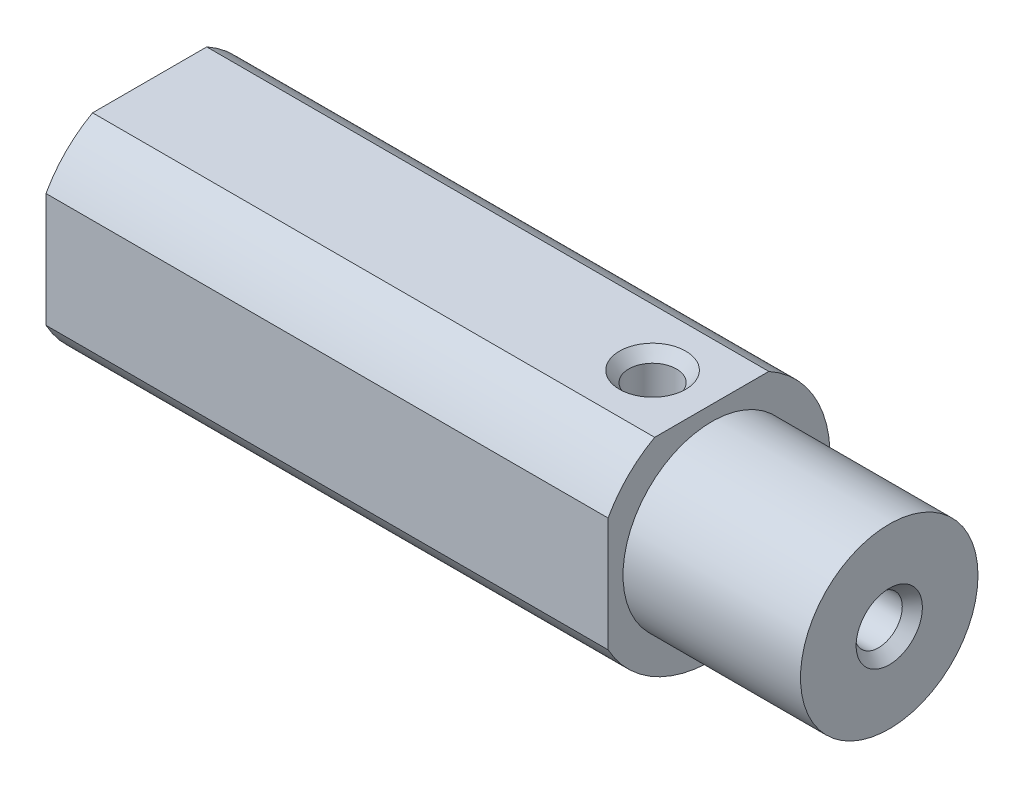
SolidWorks part; units mm, degrees
ref_plane "Front Plane" through (0, 0, 0) normal (0, 0, 1) x (1, 0, 0)
ref_plane "Top Plane" through (0, 0, 0) normal (0, 1, 0) x (1, 0, 0)
ref_plane "Right Plane" through (0, 0, 0) normal (1, 0, 0) x (0, 0, -1)
sketch "Sketch1" plane through (0, 0, 0) normal (1, 0, 0) x (0, 0, -1)
  circle A0 centre (0, 0) radius 12.7
extrude "Boss-Extrude1" add sketch "Sketch1" against normal blind 79.375
sketch "Sketch2" plane through (0, 0, 0) normal (1, 0, 0) x (0, 0, -1)
  circle A0 centre (0, 0) radius 9.525
  circle A1 centre (0, 0) radius 21.2934
extrude "Cut-Extrude1" cut sketch "Sketch2" against normal blind 19.05
ref_plane "Plane1" through (0, 0, 11.1252) normal (0, 0, 1) x (1, 0, 0)
sketch "Sketch3" plane through (0, 12.4012, 11.1252) normal (0, 0, 1) x (1, 0, 0)
  line L1 (-91.2436, 24.1614) -> (-2.896, 24.1614)
  line L2 (-91.2436, 24.1614) -> (-91.2436, -37.9233)
  line L3 (-91.2436, -37.9233) -> (-2.896, -37.9233)
  line L4 (-2.896, 24.1614) -> (-2.896, -37.9233)
extrude "Cut-Extrude2" cut sketch "Sketch3" along normal blind 7.62
ref_plane "Plane3" through (0, 11.1252, 0) normal (0, 1, 0) x (-1, 0, 0)
sketch "Sketch7" plane through (0, 11.1252, 0) normal (0, 1, 0) x (-1, 0, 0)
  line L1 (96.4133, -27.0383) -> (-22.4115, -27.0383)
  line L2 (96.4133, -27.0383) -> (96.4133, 24.8097)
  line L3 (96.4133, 24.8097) -> (-22.4115, 24.8097)
  line L4 (-22.4115, -27.0383) -> (-22.4115, 24.8097)
extrude "Cut-Extrude5" cut sketch "Sketch7" along normal blind 25.4
hole_wizard "1/4-20 Tapped Hole2" positions "Sketch15" profile "Sketch14" tap size "1/4-20" standard "Ansi Inch"
sketch "Sketch15" plane through (0, 11.1252, 0) normal (0, 1, 0) x (-1, 0, 0)
  line L0 (0, 13.1039) -> (0, -13.1039) construction
  line L1 (13.1039, 11.1252) -> (-13.1039, 11.1252) construction
  point P0 (25.4, 0)
  dimension "D1" = 25.4
  dimension "D2" = 11.1252
sketch "Sketch14" plane through (-25.4, 11.1252, 0) normal (1, 0, 0) x (0, 0, 1)
  line L0 (0, 0) -> (0, 17.5358)
  line L1 (0, 17.5358) -> (2.5527, 16.002)
  line L2 (2.5527, 16.002) -> (2.5527, 1.1542)
  line L3 (2.5527, 1.1542) -> (3.556, 0)
  line L5 (3.556, 0) -> (0, 0)
  line L6 (-2.5527, 1.1542) -> (-3.556, 0) construction
  line L10 (0, 17.5358) -> (-2.5527, 16.002) construction
  line L11 (0, -6.35) -> (0, 107.95) construction
  dimension "Tap Drill Dia." = 5.1054
  dimension "Tap Drill Depth" = 16.002
  dimension "Near C'Sink Dia." = 7.112
  dimension "Near C'Sink Angle" = 82
  dimension "Drill Angle" = 118
cosmetic thread "Hole Thread2" parameters "D1"=12.7, "D2"=6.35
hole_wizard "1/4-20 Tapped Hole3" positions "Sketch17" profile "Sketch16" tap size "1/4-20" standard "Ansi Inch"
sketch "Sketch17" plane through (0, 0, 0) normal (1, 0, 0) x (0, 0, -1)
  point P0 (0, 0)
sketch "Sketch16" plane through (0, 0, 0) normal (0, 1, 0) x (0, 0, -1)
  line L0 (0, 0) -> (0, 17.5358)
  line L1 (0, 17.5358) -> (2.5527, 16.002)
  line L2 (2.5527, 16.002) -> (2.5527, 1.1542)
  line L3 (2.5527, 1.1542) -> (3.556, 0)
  line L5 (3.556, 0) -> (0, 0)
  line L6 (-2.5527, 1.1542) -> (-3.556, 0) construction
  line L10 (0, 17.5358) -> (-2.5527, 16.002) construction
  line L11 (0, -6.35) -> (0, 107.95) construction
  dimension "Tap Drill Dia." = 5.1054
  dimension "Tap Drill Depth" = 16.002
  dimension "Near C'Sink Dia." = 7.112
  dimension "Near C'Sink Angle" = 82
  dimension "Drill Angle" = 118
cosmetic thread "Hole Thread3" parameters "D1"=12.7, "D2"=6.35
